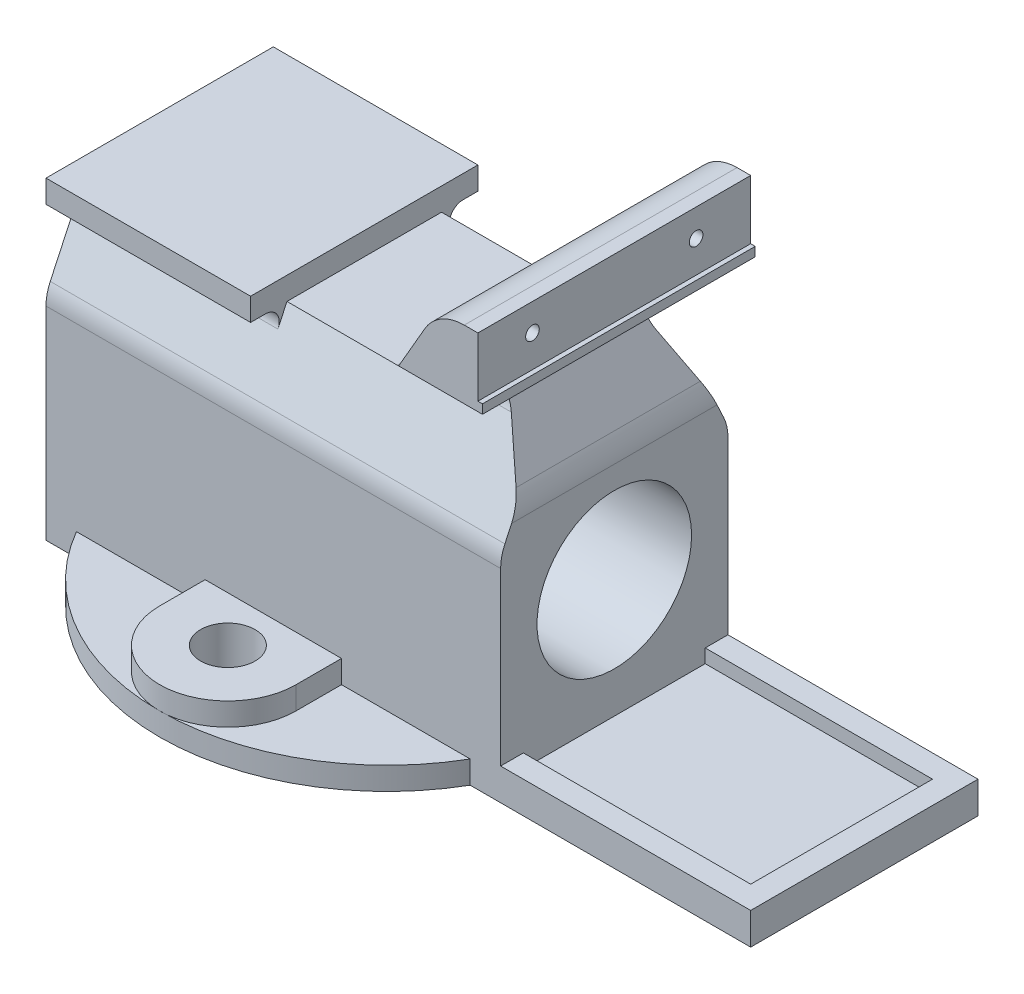
SolidWorks part; units mm, degrees
material "AISI 304"
ref_plane "Front Plane" through (0, 0, 0) normal (0, 0, 1) x (1, 0, 0)
ref_plane "Top Plane" through (0, 0, 0) normal (0, 1, 0) x (1, 0, 0)
ref_plane "Right Plane" through (0, 0, 0) normal (1, 0, 0) x (0, 0, -1)
sketch "Sketch17" plane through (0, 0, 0) normal (0, 1, 0) x (1, 0, 0)
  circle A0 centre (0, 0) radius 50
  dimension "D1" = 100
extrude "Boss-Extrude9" add sketch "Sketch17" along normal blind 5 contours A0
sketch "Sketch2" plane through (0, 5, 0) normal (0, -1, 0) x (1, 0, 0)
  line L0 (0, -35) -> (0, 35) construction
  line L1 (-15, -35) -> (-15, 35)
  line L2 (15, -35) -> (15, 35)
  arc A0 (-15, -35) -> (15, -35) centre (0, -35) ccw
  arc A1 (15, 35) -> (-15, 35) centre (0, 35) ccw
  point P3 (0, 0)
  dimension "D2" = 15
  dimension "D1" = 70
extrude "Boss-Extrude1" add sketch "Sketch2" against normal blind 5
sketch "Sketch3" plane through (0, 10, 0) normal (0, 1, 0) x (1, 0, 0)
  circle A0 centre (0, 35) radius 6
  circle A1 centre (0, -35) radius 6
  dimension "D1" = 12
extrude "Cut-Extrude1" cut sketch "Sketch3" against normal through all
sketch "Sketch5" plane through (0, 0, 0) normal (1, 0, 0) x (0, 0, -1)
  line L0 (0, 0) -> (0, 70.9957) construction
  line L1 (17, 64) -> (-17, 64)
  line L2 (25, 44.627) -> (25, 0)
  line L3 (-24.0631, 48.8532) -> (-17, 64)
  line L4 (24.0631, 48.8532) -> (17, 64)
  line L20 (-25, 44.627) -> (-25, 0)
  line L21 (-25, 0) -> (25, 0)
  arc A0 (24.0631, 48.8532) -> (25, 44.627) centre (15, 44.627) cw
  arc A11 (-24.0631, 48.8532) -> (-25, 44.627) centre (-15, 44.627) ccw
  point P12 (0, 64)
  dimension "D3" = 10
  dimension "D2" = 34
  dimension "D1" = 64
  dimension "D4" = 25
  dimension "D5" = 50
extrude "Boss-Extrude3" add sketch "Sketch5" along normal mid plane 100
sketch "Sketch4" plane through (-50, 0, 0) normal (1, 0, 0) x (0, 0, -1)
  line L0 (-17, 64) -> (-18.9901, 59.7321)
  line L1 (25, 69) -> (-25, 69)
  line L2 (-25, 69) -> (-25, 64)
  line L6 (-25, 64) -> (-21.7091, 64)
  line L8 (0, 0) -> (0, 88.6242) construction
  line L9 (24.0631, 48.8532) -> (17, 64) construction
  line L12 (25, 64) -> (21.7091, 64)
  line L14 (25, 69) -> (25, 64)
  line L15 (24.0631, 48.8532) -> (17, 64) construction
  line L17 (17, 64) -> (-17, 64) construction
  line L19 (17, 64) -> (-17, 64)
  line L20 (18.9901, 59.7321) -> (17, 64)
  arc A0 (-21.7091, 64) -> (-18.9901, 59.7321) centre (-21.7091, 61) cw
  arc A4 (21.7091, 64) -> (18.9901, 59.7321) centre (21.7091, 61) ccw
  point P28 (0, 69)
  dimension "D9" = 3
  dimension "D1" = 50
  dimension "D7" = 5
sketch "Sketch6" plane through (0, 0, 25) normal (0, 0, 1) x (1, 0, 0)
  line L0 (50, 7) -> (50, 0)
  line L4 (105, 0) -> (105, 7)
  line L5 (105, 7) -> (50, 7)
  line L7 (0, 0) -> (138.7494, 0) construction
  line L8 (50, 44.627) -> (50, 0) construction
  line L9 (50, 0) -> (105, 0)
  dimension "D1" = 55
  dimension "D3" = 7
extrude "Boss-Extrude7" add sketch "Sketch4" along normal blind 45
extrude "Boss-Extrude4" add sketch "Sketch6" against normal up to surface (50 mm away) up to face at (0, 10.7712, -25)
sketch "Sketch7" plane through (0, 0, 0) normal (0, 0, 1) x (1, 0, 0)
  line L0 (50, 64) -> (50, 92)
  line L4 (25.0607, 64) -> (50, 64)
  line L5 (25.0607, 64) -> (38.3397, 87)
  line L6 (50, 64) -> (-5, 64) construction
  line L7 (50, 92) -> (47, 92)
  arc A2 (38.3397, 87) -> (47, 92) centre (47, 82) cw
  point P5 (41.2265, 92)
  dimension "D1" = 3
  dimension "D6" = 10
  dimension "D3" = 92
  dimension "D4" = 120
extrude "Boss-Extrude5" add sketch "Sketch7" along normal mid plane 60 contours L0 L7 A2 L5 L4
sketch "Sketch8" plane through (0, 0, 30) normal (0, 0, 1) x (1, 0, 0)
  line L0 (50, 52) -> (50, 77)
  line L1 (50, 64) -> (50, 92) construction
  line L3 (50, 77) -> (45.7735, 77)
  line L4 (41.4434, 69.5) -> (48.6603, 57)
  arc A0 (45.7735, 77) -> (41.4434, 69.5) centre (45.7735, 72) ccw
  arc A1 (50, 52) -> (48.6603, 57) centre (40, 52) ccw
  dimension "D1" = 10
  dimension "D3" = 5
  dimension "D2" = 15
  dimension "D4" = 30
  dimension "D5" = 40
extrude "Cut-Extrude2" cut sketch "Sketch8" against normal through all
sketch "Sketch10" plane through (50, 0, 0) normal (1, 0, 0) x (0, 0, -1)
  line L0 (0, 0) -> (0, 100.0467) construction
  line L1 (30, 77) -> (30, 36.1214)
  line L2 (30, 36.1214) -> (15.859, 66.447)
  line L4 (30, 77) -> (22.582, 77)
  line L5 (-30, 77) -> (-22.582, 77)
  line L6 (-30, 36.1214) -> (-15.859, 66.447)
  line L7 (-30, 77) -> (-30, 36.1214)
  line L8 (24.0631, 48.8532) -> (22.5957, 52) construction
  line L9 (30, 77) -> (-30, 77) construction
  arc A0 (22.582, 77) -> (15.859, 66.447) centre (22.582, 69.582) ccw
  arc A1 (-22.582, 77) -> (-15.859, 66.447) centre (-22.582, 69.582) cw
extrude "Cut-Extrude4" cut sketch "Sketch10" against normal up to next
sketch "Sketch12" plane through (50, 0, 0) normal (1, 0, 0) x (0, 0, -1)
  line L0 (30, 77) -> (30, 92) construction
  line L1 (-30, 77) -> (30, 77)
  line L2 (-30, 77) -> (-30, 79)
  line L3 (-30, 79) -> (30, 79)
  line L4 (30, 77) -> (30, 79)
  point P5 (30, 78)
  dimension "D1" = 2
extrude "Boss-Extrude6" add sketch "Sketch12" along normal blind 1
sketch "Sketch14" plane through (50, 0, 0) normal (1, 0, 0) x (0, 0, -1)
  circle A0 centre (0, 30) radius 17
  dimension "D2" = 34
  dimension "D1" = 30
extrude "Cut-Extrude7" cut sketch "Sketch14" against normal through all
sketch "Sketch15" plane through (50, 0, 0) normal (1, 0, 0) x (0, 0, -1)
  line L0 (0, 0) -> (0, 104.8859) construction
  line L1 (-30, 92) -> (30, 92) construction
  circle A0 centre (-18, 86) radius 1.5
  circle A1 centre (18, 86) radius 1.5
  dimension "D2" = 3
  dimension "D1" = 36
  dimension "D3" = 6
extrude "Cut-Extrude8" cut sketch "Sketch15" against normal blind 5
sketch "Sketch18" plane through (0, 7, 0) normal (0, 1, 0) x (1, 0, 0)
  line L6 (50, 20) -> (50, -20)
  line L9 (100, 20) -> (100, -20)
  line L10 (100, -20) -> (50, -20)
  line L11 (50, 20) -> (100, 20)
  line L12 (100, 20) -> (100, -20)
  line L13 (100, -20) -> (50, -20)
  line L14 (50, 20) -> (100, 20)
  dimension "D1" = 5
extrude "Cut-Extrude9" cut sketch "Sketch18" against normal blind 3
fillet "Fillet1" radius 10 1 edges at (25.0607, 64, 0)
